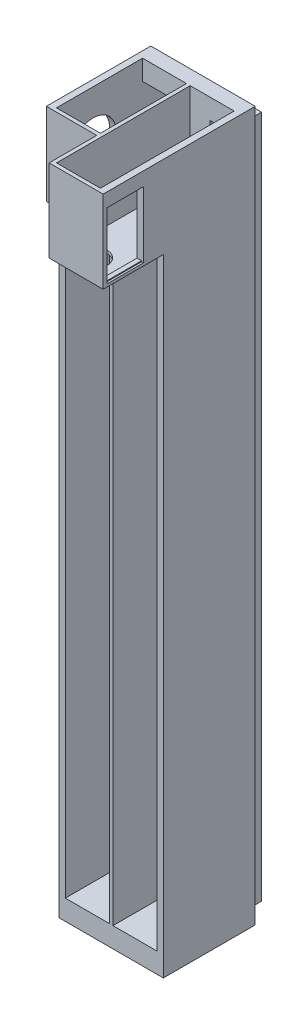
SolidWorks part; units mm, degrees
material "ABS"
ref_plane "Płaszczyzna przednia" through (0, 0, 0) normal (0, 0, 1) x (1, 0, 0)
ref_plane "Płaszczyzna górna" through (0, 0, 0) normal (0, 1, 0) x (1, 0, 0)
ref_plane "Płaszczyzna prawa" through (0, 0, 0) normal (1, 0, 0) x (0, 0, -1)
sketch "Szkic1" plane through (0, 0, 0) normal (0, 0, 1) x (1, 0, 0)
  line L0 (-90.4269, 49.2609) -> (-90.4269, -315.7391)
  line L1 (-91.9269, 53.7609) -> (-38.9269, 53.7609)
  line L2 (-91.9269, 53.7609) -> (-91.9269, -320.2391)
  line L3 (-91.9269, -320.2391) -> (-38.9269, -320.2391)
  line L4 (-38.9269, 53.7609) -> (-38.9269, -320.2391)
  line L5 (-40.4269, 49.2609) -> (-64.4269, 49.2609)
  line L6 (-90.4269, -315.7391) -> (-66.4269, -315.7391)
  line L7 (-90.4269, 49.2609) -> (-66.4269, 49.2609)
  line L8 (-66.4269, 49.2609) -> (-66.4269, -315.7391)
  line L10 (-64.4269, 49.2609) -> (-64.4269, -315.7391)
  line L13 (-40.4269, 49.2609) -> (-40.4269, -315.7391)
  line L14 (-40.4269, -315.7391) -> (-64.4269, -315.7391)
  dimension "D1" = 374
  dimension "D2" = 24
  dimension "D3" = 53
  dimension "D4" = 365
extrude "Dodanie-wyciągnięcie2" add sketch "Szkic1" along normal blind 12 contours L3 L4 L1 L2 | L6 L8 L7 L0 | L14 L10 L5 L13
sketch "Szkic2" plane through (-66.4269, 0, 0) normal (-1, 0, 0) x (0, 0, 1)
  line L0 (12, 49.2609) -> (12, -315.7391) construction
  line L1 (0, 49.2609) -> (12, 49.2609)
  line L2 (0, 49.2609) -> (0, 45.7609)
  line L3 (0, 45.7609) -> (12, 45.7609)
  line L4 (12, 49.2609) -> (12, 45.7609)
extrude "Wytnij-wyciągnięcie1" cut sketch "Szkic2" against normal blind 2
ref_plane "Płaszczyzna1" through (0, 0, 12) normal (0, 0, 1) x (1, 0, 0)
sketch "Szkic3" plane through (0, 0, 12) normal (0, 0, 1) x (1, 0, 0)
  line L6 (-38.9269, -320.2391) -> (-91.9269, -320.2391)
  line L7 (-38.9269, -320.2391) -> (-38.9269, 53.7609)
  line L8 (-38.9269, 53.7609) -> (-91.9269, 53.7609)
  line L9 (-91.9269, -320.2391) -> (-91.9269, 53.7609)
extrude "Dodanie-wyciągnięcie3" add sketch "Szkic3" along normal blind 2
sketch "Szkic4" plane through (0, 0, 14) normal (0, 0, 1) x (1, 0, 0)
  line L64 (-46.9269, -11.0391) -> (-56.3269, -11.0391)
  line L69 (-90.4269, 49.2609) -> (-40.4269, 49.2609) construction
  line L70 (-53.7269, 49.2609) -> (-40.4269, 49.2609)
  line L71 (-40.4269, 49.2609) -> (-40.4269, 18.7608)
  line L72 (-40.4269, 49.2609) -> (-40.4269, -315.7391) construction
  line L73 (-40.4269, 18.7608) -> (-53.7269, 18.7608)
  line L74 (-53.7269, 49.2609) -> (-53.7269, 18.7608)
  line L77 (-77.1269, 49.2609) -> (-77.1269, 18.7608)
  line L78 (-90.4269, 18.7608) -> (-77.1269, 18.7608)
  line L79 (-90.4269, 49.2609) -> (-90.4269, 18.7608)
  line L80 (-77.1269, 49.2609) -> (-90.4269, 49.2609)
  line L81 (-74.5269, -35.3991) -> (-74.5269, -40.4791)
  line L82 (-74.5269, -40.4791) -> (-83.9269, -40.4791)
  line L87 (-46.9269, -35.3991) -> (-46.9269, -11.0391)
  line L89 (-56.3269, -35.3991) -> (-56.3269, -11.0391)
  line L90 (-74.5269, -35.3991) -> (-74.5269, -11.0391)
  line L92 (-83.9269, -35.3991) -> (-83.9269, -11.0391)
  line L93 (-83.9269, -11.0391) -> (-74.5269, -11.0391)
  line L94 (-46.9269, -101.2391) -> (-46.9269, -166.1991)
  line L95 (-46.9269, -166.1991) -> (-56.3269, -166.1991)
  line L96 (-46.9269, -101.2391) -> (-56.3269, -101.2391)
  line L97 (-56.3269, -166.1991) -> (-56.3269, -101.2391)
  line L98 (-74.5269, -166.1991) -> (-74.5269, -101.2391)
  line L99 (-83.9269, -101.2391) -> (-74.5269, -101.2391)
  line L100 (-83.9269, -166.1991) -> (-74.5269, -166.1991)
  line L101 (-83.9269, -101.2391) -> (-83.9269, -166.1991)
  line L102 (-83.9269, -40.4791) -> (-83.9269, -35.3991)
  line L103 (-56.3269, -35.3991) -> (-56.3269, -40.4791)
  line L104 (-56.3269, -40.4791) -> (-46.9269, -40.4791)
  line L105 (-46.9269, -40.4791) -> (-46.9269, -35.3991)
extrude "Wytnij-wyciągnięcie2" cut sketch "Szkic4" against normal blind 2
sketch "Szkic5" plane through (0, 0, 14) normal (0, 0, 1) x (1, 0, 0)
  line L1 (-91.9269, -320.2391) -> (-38.9269, -320.2391) construction
  line L7 (-64.4269, -320.2391) -> (-66.4269, -320.2391)
  line L11 (-64.4269, -320.2391) -> (-64.4269, 53.7609)
  line L12 (-64.4269, 53.7609) -> (-66.4269, 53.7609)
  line L13 (-66.4269, -320.2391) -> (-66.4269, 53.7609)
extrude "Dodanie-wyciągnięcie4" add sketch "Szkic5" along normal blind 43
sketch "Szkic6" plane through (0, 0, 14) normal (0, 0, 1) x (1, 0, 0)
  line L0 (-64.4269, 16.7608) -> (-40.4269, 16.7608)
  line L4 (-64.4269, -320.2391) -> (-64.4269, 53.7609) construction
  line L5 (-40.4269, 49.2609) -> (-40.4269, -315.7391) construction
  line L6 (-40.4269, 16.7608) -> (-40.4269, 53.7609)
  line L7 (-91.9269, 53.7609) -> (-38.9269, 53.7609) construction
  line L8 (-40.4269, 53.7609) -> (-38.9269, 53.7609)
  line L19 (-90.4269, 53.7609) -> (-91.9269, 53.7609)
  line L20 (-90.4269, 16.7608) -> (-90.4269, 53.7609)
  line L21 (-66.4269, 16.7608) -> (-90.4269, 16.7608)
  line L22 (-64.4269, 16.7608) -> (-64.4269, 15.2608)
  line L23 (-64.4269, 15.2608) -> (-38.9269, 15.2608)
  line L24 (-38.9269, 15.2608) -> (-38.9269, 53.7609)
  line L25 (-91.9269, 15.2608) -> (-91.9269, 53.7609)
  line L26 (-66.4269, 15.2608) -> (-91.9269, 15.2608)
  line L27 (-66.4269, 16.7608) -> (-66.4269, 15.2608)
extrude "Dodanie-wyciągnięcie5" add sketch "Szkic6" along normal blind 41.5
ref_plane "Płaszczyzna2" through (0, 0, 55.5) normal (0, 0, 1) x (1, 0, 0)
sketch "Szkic7" plane through (0, 0, 55.5) normal (0, 0, 1) x (1, 0, 0)
  line L1 (-38.9269, 15.2608) -> (-64.4269, 15.2608)
  line L2 (-38.9269, 15.2608) -> (-38.9269, 53.7609)
  line L3 (-38.9269, 53.7609) -> (-64.4269, 53.7609)
  line L4 (-64.4269, 15.2608) -> (-64.4269, 53.7609)
  line L5 (-66.4269, 15.2608) -> (-91.9269, 15.2608)
  line L6 (-66.4269, 15.2608) -> (-66.4269, 53.7609)
  line L7 (-66.4269, 53.7609) -> (-91.9269, 53.7609)
  line L8 (-91.9269, 15.2608) -> (-91.9269, 53.7609)
extrude "Dodanie-wyciągnięcie6" add sketch "Szkic7" along normal blind 1.5
sketch "Szkic10" plane through (0, 0, 14) normal (0, 0, 1) x (1, 0, 0)
  line L0 (-91.9269, 15.2608) -> (-91.9269, -320.2391)
  line L1 (-91.9269, -320.2391) -> (-66.4269, -320.2391)
  line L2 (-66.4269, -320.2391) -> (-66.4269, -315.7391)
  line L3 (-66.4269, 15.2608) -> (-66.4269, -320.2391) construction
  line L4 (-66.4269, -315.7391) -> (-90.4269, -315.7391)
  line L5 (-90.4269, -315.7391) -> (-90.4269, 15.2608)
  line L6 (-91.9269, 15.2608) -> (-66.4269, 15.2608) construction
  line L7 (-90.4269, 15.2608) -> (-91.9269, 15.2608)
  dimension "D1" = 24
  dimension "D2" = 330.9999
extrude "Dodanie-wyciągnięcie7" add sketch "Szkic10" along normal blind 43
sketch "Szkic11" plane through (0, 0, 14) normal (0, 0, 1) x (1, 0, 0)
  line L0 (-38.9269, 15.2608) -> (-38.9269, -320.2391)
  line L1 (-38.9269, -320.2391) -> (-64.4269, -320.2391)
  line L2 (-64.4269, -320.2391) -> (-64.4269, -315.7391)
  line L3 (-64.4269, -320.2391) -> (-64.4269, 15.2608) construction
  line L4 (-64.4269, -315.7391) -> (-40.4269, -315.7391)
  line L5 (-40.4269, -315.7391) -> (-40.4269, 15.2608)
  line L6 (-64.4269, 15.2608) -> (-38.9269, 15.2608) construction
  line L7 (-40.4269, 15.2608) -> (-38.9269, 15.2608)
  dimension "D1" = 330.9999
  dimension "D2" = 24
extrude "Dodanie-wyciągnięcie8" add sketch "Szkic11" along normal blind 43
sketch "Szkic15" plane through (-91.9269, 0, 0) normal (-1, 0, 0) x (0, 0, 1)
  line L1 (57, 53.7609) -> (0, 53.7609)
  line L2 (57, 53.7609) -> (57, -320.2391)
  line L3 (57, -320.2391) -> (0, -320.2391)
  line L4 (0, 53.7609) -> (0, -320.2391)
extrude "Dodanie-wyciągnięcie10" add sketch "Szkic15" along normal blind 1
sketch "Szkic16" plane through (-38.9269, 0, 0) normal (1, 0, 0) x (0, 0, -1)
  line L1 (-57, -320.2391) -> (0, -320.2391)
  line L2 (-57, -320.2391) -> (-57, 53.7609)
  line L3 (-57, 53.7609) -> (0, 53.7609)
  line L4 (0, -320.2391) -> (0, 53.7609)
extrude "Dodanie-wyciągnięcie11" add sketch "Szkic16" along normal blind 1
sketch "Szkic17" plane through (0, 53.7609, 0) normal (0, 1, 0) x (1, 0, 0)
  line L1 (-37.9269, -57) -> (-92.9269, -57)
  line L2 (-37.9269, -57) -> (-37.9269, 0)
  line L3 (-37.9269, 0) -> (-92.9269, 0)
  line L4 (-92.9269, -57) -> (-92.9269, 0)
  line L5 (-40.4269, -55.5) -> (-64.4269, -55.5)
  line L6 (-40.4269, -55.5) -> (-40.4269, -14)
  line L7 (-40.4269, -14) -> (-64.4269, -14)
  line L8 (-64.4269, -55.5) -> (-64.4269, -14)
  line L9 (-66.4269, -55.5) -> (-90.4269, -55.5)
  line L10 (-66.4269, -55.5) -> (-66.4269, -14)
  line L11 (-66.4269, -14) -> (-90.4269, -14)
  line L12 (-90.4269, -55.5) -> (-90.4269, -14)
extrude "Dodanie-wyciągnięcie12" add sketch "Szkic17" along normal blind 1
sketch "Szkic18" plane through (0, -320.2391, 0) normal (0, -1, 0) x (1, 0, 0)
  line L1 (-92.9269, 57) -> (-37.9269, 57)
  line L2 (-92.9269, 57) -> (-92.9269, 0)
  line L3 (-92.9269, 0) -> (-37.9269, 0)
  line L4 (-37.9269, 57) -> (-37.9269, 0)
extrude "Dodanie-wyciągnięcie13" add sketch "Szkic18" along normal blind 1
sketch "Szkic19" plane through (0, 0, 0) normal (0, 0, -1) x (-1, 0, 0)
  line L1 (37.9269, -321.2391) -> (92.9269, -321.2391)
  line L2 (37.9269, -321.2391) -> (37.9269, 54.7609)
  line L3 (37.9269, 54.7609) -> (92.9269, 54.7609)
  line L4 (92.9269, -321.2391) -> (92.9269, 54.7609)
  line L8 (91.4269, -319.7391) -> (39.4269, -319.7391)
  line L9 (91.4269, -319.7391) -> (91.4269, 53.2609)
  line L10 (91.4269, 53.2609) -> (39.4269, 53.2609)
  line L11 (39.4269, -319.7391) -> (39.4269, 53.2609)
extrude "Wytnij-wyciągnięcie7" cut sketch "Szkic19" against normal blind 6
sketch "Szkic23" plane through (0, 0, 57) normal (0, 0, 1) x (1, 0, 0)
  line L6 (-40.4269, 54.7609) -> (-64.4269, 54.7609)
  line L16 (-40.4269, 16.7608) -> (-64.4269, 16.7608)
  line L17 (-64.4269, 54.7609) -> (-64.4269, 16.7608)
  line L18 (-40.4269, 16.7608) -> (-40.4269, 54.7609)
  line L21 (-90.4269, 16.7608) -> (-66.4269, 16.7608)
  line L22 (-90.4269, 16.7608) -> (-90.4269, 54.7609)
  line L23 (-66.4269, 54.7609) -> (-66.4269, 16.7608)
  line L24 (-90.4269, 54.7609) -> (-66.4269, 54.7609)
extrude "Wytnij-wyciągnięcie11" cut sketch "Szkic23" against normal blind 10
sketch "Szkic24" plane through (0, 0, 57) normal (0, 0, 1) x (1, 0, 0)
  line L0 (-40.4269, 54.7609) -> (-37.9269, 54.7609)
  line L2 (-37.9269, 54.7609) -> (-37.9269, -321.2391) construction
  line L3 (-37.9269, 15.2608) -> (-37.9269, 54.7609)
  line L9 (-66.4269, 16.7608) -> (-66.4269, 54.7609)
  line L10 (-66.4269, 54.7609) -> (-64.4269, 54.7609)
  line L11 (-64.4269, 54.7609) -> (-64.4269, 16.7608)
  line L12 (-64.4269, 16.7608) -> (-40.4269, 16.7608)
  line L13 (-40.4269, 16.7608) -> (-40.4269, 54.7609)
  line L14 (-66.4269, 16.7608) -> (-66.4269, 15.2608)
  line L15 (-66.4269, 15.2608) -> (-37.9269, 15.2608)
extrude "Dodanie-wyciągnięcie14" add sketch "Szkic24" along normal blind 32
sketch "Szkic25" plane through (0, 16.7608, 0) normal (0, 1, 0) x (1, 0, 0)
  line L0 (-64.4269, -89) -> (-64.4269, -14) construction
  line L1 (-40.4269, -89) -> (-64.4269, -89)
  line L2 (-40.4269, -89) -> (-40.4269, -87)
  line L3 (-40.4269, -87) -> (-64.4269, -87)
  line L4 (-64.4269, -89) -> (-64.4269, -87)
extrude "Dodanie-wyciągnięcie15" add sketch "Szkic25" along normal blind 38
sketch "Szkic27" plane through (0, 15.2608, 0) normal (0, -1, 0) x (1, 0, 0)
  circle A7 centre (-52.6769, 78) radius 7
extrude "Wytnij-wyciągnięcie12" cut sketch "Szkic27" against normal blind 10
sketch "Szkic29" plane through (-37.9269, 0, 0) normal (1, 0, 0) x (0, 0, -1)
  line L2 (-87, 17.2608) -> (-67, 17.2608)
  line L9 (-87, 17.2608) -> (-87, 52.7608)
  line L10 (-87, 52.7608) -> (-67, 52.7608)
  line L11 (-67, 17.2608) -> (-67, 52.7608)
extrude "Wytnij-wyciągnięcie13" cut sketch "Szkic29" against normal blind 3
sketch "Szkic30" plane through (0, 0, 57) normal (0, 0, 1) x (1, 0, 0)
  line L0 (-66.4269, 16.7608) -> (-66.4269, 15.2608)
  line L1 (-66.4269, 15.2608) -> (-92.9269, 15.2608)
  line L2 (-92.9269, -321.2391) -> (-92.9269, 54.7609) construction
  line L3 (-92.9269, 15.2608) -> (-92.9269, 54.7609)
  line L4 (-92.9269, 54.7609) -> (-90.4269, 54.7609)
  line L5 (-90.4269, 54.7609) -> (-90.4269, 16.7608)
  line L6 (-90.4269, 16.7608) -> (-66.4269, 16.7608)
extrude "Dodanie-wyciągnięcie16" add sketch "Szkic30" along normal blind 6
sketch "Szkic31" plane through (0, 16.7608, 0) normal (0, 1, 0) x (1, 0, 0)
  line L0 (-66.4269, -89) -> (-66.4269, -14) construction
  line L1 (-90.4269, -63) -> (-66.4269, -63)
  line L2 (-90.4269, -63) -> (-90.4269, -61)
  line L3 (-90.4269, -61) -> (-66.4269, -61)
  line L4 (-66.4269, -63) -> (-66.4269, -61)
extrude "Dodanie-wyciągnięcie17" add sketch "Szkic31" along normal blind 38
sketch "Szkic32" plane through (-92.9269, 0, 0) normal (-1, 0, 0) x (0, 0, 1)
  circle A3 centre (41, 33.0109) radius 12.5
extrude "Wytnij-wyciągnięcie14" cut sketch "Szkic32" against normal blind 3
sketch "Szkic33" plane through (0, 54.7609, 0) normal (0, 1, 0) x (1, 0, 0)
  line L0 (-37.9269, -89) -> (-66.4269, -89)
  line L1 (-66.4269, -89) -> (-66.4269, -63)
  line L2 (-66.4269, -63) -> (-92.9269, -63)
  line L3 (-92.9269, -63) -> (-92.9269, -6)
  line L4 (-92.9269, -6) -> (-37.9269, -6)
  line L5 (-37.9269, -6) -> (-37.9269, -89)
  line L7 (-40.4269, -87) -> (-64.4269, -87)
  line L8 (-40.4269, -87) -> (-40.4269, -14)
  line L9 (-40.4269, -14) -> (-64.4269, -14)
  line L10 (-64.4269, -87) -> (-64.4269, -14)
  line L11 (-66.4269, -61) -> (-90.4269, -61)
  line L12 (-66.4269, -61) -> (-66.4269, -14)
  line L13 (-66.4269, -14) -> (-90.4269, -14)
  line L14 (-90.4269, -61) -> (-90.4269, -14)
extrude "Dodanie-wyciągnięcie18" add sketch "Szkic33" along normal blind 5.5
sketch "Szkic34" plane through (0, -321.2391, 0) normal (0, -1, 0) x (1, 0, 0)
  line L1 (-92.9269, 57) -> (-37.9269, 57)
  line L2 (-92.9269, 57) -> (-92.9269, 6)
  line L3 (-92.9269, 6) -> (-37.9269, 6)
  line L4 (-37.9269, 57) -> (-37.9269, 6)
extrude "Dodanie-wyciągnięcie19" add sketch "Szkic34" along normal blind 5.5
sketch "Szkic35" plane through (-37.9269, 0, 0) normal (1, 0, 0) x (0, 0, -1)
  line L0 (-57, -326.7391) -> (-57, 15.2608)
  line L1 (-57, 15.2608) -> (-89, 15.2608)
  line L2 (-89, 15.2608) -> (-89, 60.2609)
  line L3 (-89, 60.2609) -> (-6, 60.2609)
  line L4 (-6, 60.2609) -> (-6, -326.7391)
  line L5 (-6, -326.7391) -> (-57, -326.7391)
  line L7 (-87, 16.7608) -> (-67, 16.7608)
  line L8 (-87, 16.7608) -> (-87, 52.7608)
  line L9 (-87, 52.7608) -> (-67, 52.7608)
  line L10 (-67, 16.7608) -> (-67, 52.7608)
extrude "Dodanie-wyciągnięcie20" add sketch "Szkic35" along normal blind 1
sketch "Szkic36" plane through (-92.9269, 0, 0) normal (-1, 0, 0) x (0, 0, 1)
  line L0 (63, 60.2609) -> (63, 15.2608)
  line L1 (63, 15.2608) -> (57, 15.2608)
  line L2 (57, 15.2608) -> (57, -326.7391)
  line L3 (57, -326.7391) -> (6, -326.7391)
  line L4 (6, -326.7391) -> (6, 60.2609)
  line L5 (6, 60.2609) -> (63, 60.2609)
  circle A0 centre (41, 33.0109) radius 12.5
extrude "Dodanie-wyciągnięcie21" add sketch "Szkic36" along normal blind 1
sketch "Szkic37" plane through (0, 0, 57) normal (0, 0, 1) x (1, 0, 0)
  line L1 (-36.9269, 15.2608) -> (-93.9269, 15.2608)
  line L2 (-36.9269, 15.2608) -> (-36.9269, -326.7391)
  line L3 (-36.9269, -326.7391) -> (-93.9269, -326.7391)
  line L4 (-93.9269, 15.2608) -> (-93.9269, -326.7391)
extrude "Wytnij-wyciągnięcie15" cut sketch "Szkic37" against normal blind 0.85
